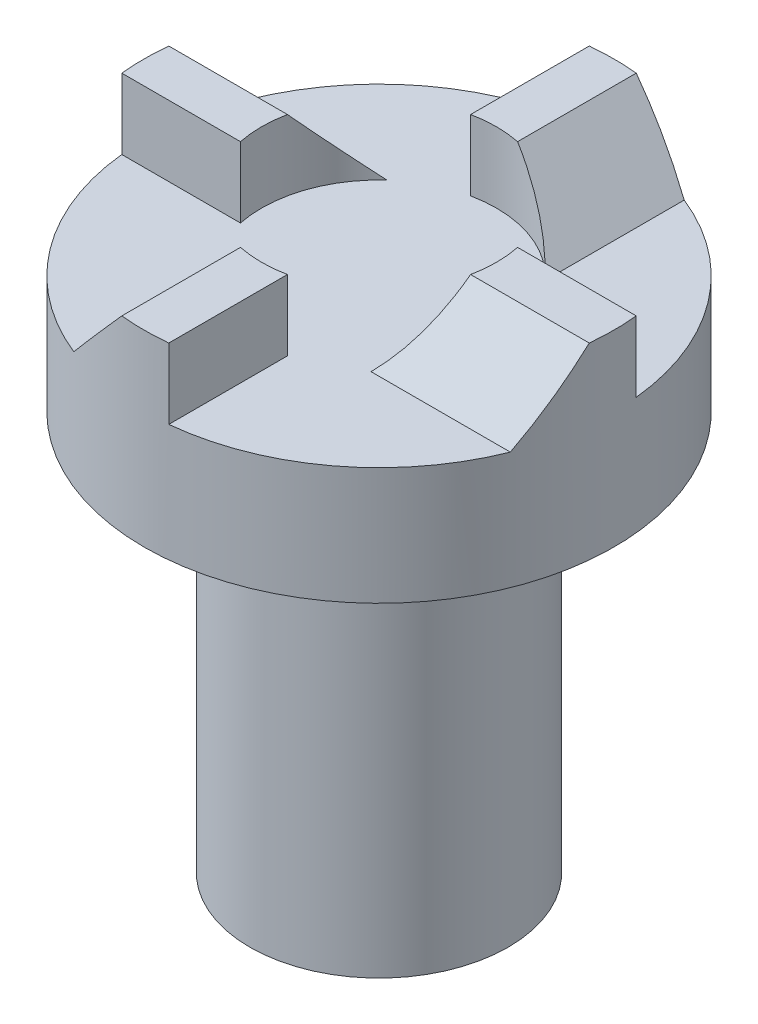
SolidWorks part; units mm, degrees
ref_plane "Front Plane" through (0, 0, 0) normal (0, 0, 1) x (1, 0, 0)
ref_plane "Top Plane" through (0, 0, 0) normal (0, 1, 0) x (1, 0, 0)
ref_plane "Right Plane" through (0, 0, 0) normal (1, 0, 0) x (0, 0, -1)
sketch "Sketch1" plane through (0, 0, 0) normal (0, 1, 0) x (1, 0, 0)
  circle A0 centre (0, 0) radius 5.5
  dimension "D1" = 11
extrude "Boss-Extrude1" add sketch "Sketch1" along normal blind 17
sketch "Sketch2" plane through (0, 17, 0) normal (0, 1, 0) x (1, 0, 0)
  circle A0 centre (0, 0) radius 10
  dimension "D1" = 20
extrude "Boss-Extrude2" add sketch "Sketch2" along normal blind 5
sketch "Sketch4" plane through (0, 22, 0) normal (0, 1, 0) x (1, 0, 0)
  line L1 (1, 10) -> (-1, 10)
  line L2 (1, 10) -> (1, 4.899)
  line L3 (1, -10) -> (-1, -10)
  line L4 (-1, 10) -> (-1, 4.899)
  line L7 (-10, 1) -> (-4.899, 1)
  line L8 (-10, 1) -> (-10, -1)
  line L9 (-10, -1) -> (-4.899, -1)
  line L10 (10, 1) -> (10, -1)
  line L20 (-1, -4.899) -> (-1, -10)
  line L23 (1, -4.899) -> (1, -10)
  line L24 (4.899, -1) -> (10, -1)
  line L27 (4.899, 1) -> (10, 1)
  arc A0 (-1, 4.899) -> (-4.899, 1) centre (0, 0) ccw
  arc A1 (-4.899, -1) -> (-1, -4.899) centre (0, 0) ccw
  arc A2 (4.899, 1) -> (1, 4.899) centre (0, 0) ccw
  arc A3 (1, -4.899) -> (4.899, -1) centre (0, 0) ccw
  circle A4 centre (0, 0) radius 10 construction
  point P1 (0, 10)
  point P12 (0, -10)
  point P13 (10, 0)
  point P15 (-10, 0)
  dimension "D1" = 10
  dimension "D2" = 20
  dimension "D3" = 2
extrude "Boss-Extrude3" add sketch "Sketch4" along normal blind 3
sketch "Sketch9" plane through (0, 0, -10) normal (0, 0, -1) x (-1, 0, 0)
  line L0 (-1, 25) -> (-3.7012, 22)
  line L1 (-1, 22) -> (-9.9499, 22) construction
  line L2 (-3.7012, 22) -> (-1, 22)
  line L3 (-1, 22) -> (-1, 25)
  dimension "D1" = 48
extrude "Boss-Extrude4" add sketch "Sketch9" against normal up to next
pattern_circular "CirPattern1" count 4 over 360 about axis through (0, 0, 0) along (0, 1, 0) of "Boss-Extrude4"
sketch "Sketch10" plane through (0, 22, 0) normal (0, 1, 0) x (1, 0, 0)
  circle A0 centre (0, 0) radius 10
  arc A1 (-1, 9.9499) -> (-9.2898, 3.7012) centre (0, 0) ccw construction
  circle A2 centre (0, 0) radius 13.3013
  arc M6 (9.9499, 1) -> (3.7012, 9.2898) centre (0, 0) ccw
  dimension "D1" = 26.6025
extrude "Cut-Extrude3" cut sketch "Sketch10" against normal through all both and the other way through all contours A2 A0 M6
fillet "Fillet1" radius 2 1 edges at (0, 17, 5.5)
sketch "Sketch11" plane through (0, 0, 0) normal (0, -1, 0) x (1, 0, 0)
  line L2 (1.6502, -2.0735) -> (1.6502, 2.0735)
  line L4 (-1.6502, -2.0735) -> (-1.6502, 2.0735)
  line L5 (1.6502, -2.0735) -> (-1.6502, 2.0735) construction
  line L6 (1.6502, 2.0735) -> (-1.6502, -2.0735) construction
  arc A0 (-1.6502, -2.0735) -> (1.6502, -2.0735) centre (0, 0) ccw
  arc A1 (1.6502, 2.0735) -> (-1.6502, 2.0735) centre (0, 0) ccw
  point P0 (0, 0)
  dimension "D2" = 5.3
  dimension "D1" = 4.147
extrude "Cut-Extrude4" cut sketch "Sketch11" against normal blind 6
sketch "Sketch12" plane through (0, 25, 0) normal (0, 1, 0) x (1, 0, 0)
  circle A0 centre (0, 0) radius 5
  dimension "D1" = 10
extrude "Cut-Extrude5" cut sketch "Sketch12" against normal up to surface (3 mm away) up to face at (5.8926, 22, -3.9017)
